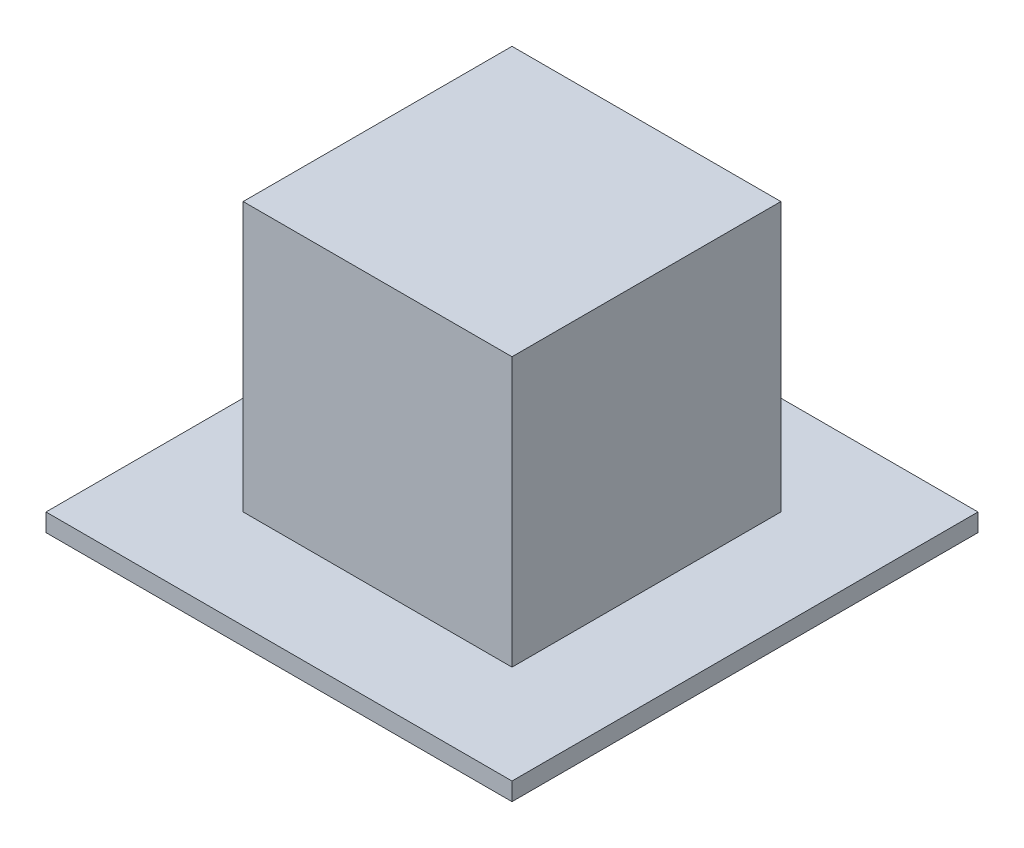
SolidWorks part; units mm, degrees
ref_plane "Front Plane" through (0, 0, 0) normal (0, 0, 1) x (1, 0, 0)
ref_plane "Top Plane" through (0, 0, 0) normal (0, 1, 0) x (1, 0, 0)
ref_plane "Right Plane" through (0, 0, 0) normal (1, 0, 0) x (0, 0, -1)
sketch "Sketch1" plane through (0, 0, 0) normal (0, 1, 0) x (1, 0, 0)
  line L1 (7.5, -7.5) -> (-7.5, -7.5)
  line L2 (7.5, -7.5) -> (7.5, 7.5)
  line L3 (7.5, 7.5) -> (-7.5, 7.5)
  line L4 (-7.5, -7.5) -> (-7.5, 7.5)
  line L5 (7.5, -7.5) -> (-7.5, 7.5) construction
  line L6 (7.5, 7.5) -> (-7.5, -7.5) construction
  point P0 (0, 0)
  dimension "D1" = 15
extrude "Boss-Extrude1" add sketch "Sketch1" along normal blind 15
sketch "Sketch2" plane through (0, 0, 0) normal (0, -1, 0) x (1, 0, 0)
  line L8 (-13, 13) -> (-13, -13)
  line L9 (-13, -13) -> (13, -13)
  line L10 (13, -13) -> (13, 13)
  line L11 (13, 13) -> (-13, 13)
  line L12 (-13, 13) -> (-13, -13)
  line L13 (-13, -13) -> (13, -13)
  line L14 (13, -13) -> (13, 13)
  line L15 (13, 13) -> (-13, 13)
  dimension "D1" = 5.5
extrude "Boss-Extrude2" add sketch "Sketch2" along normal blind 1
